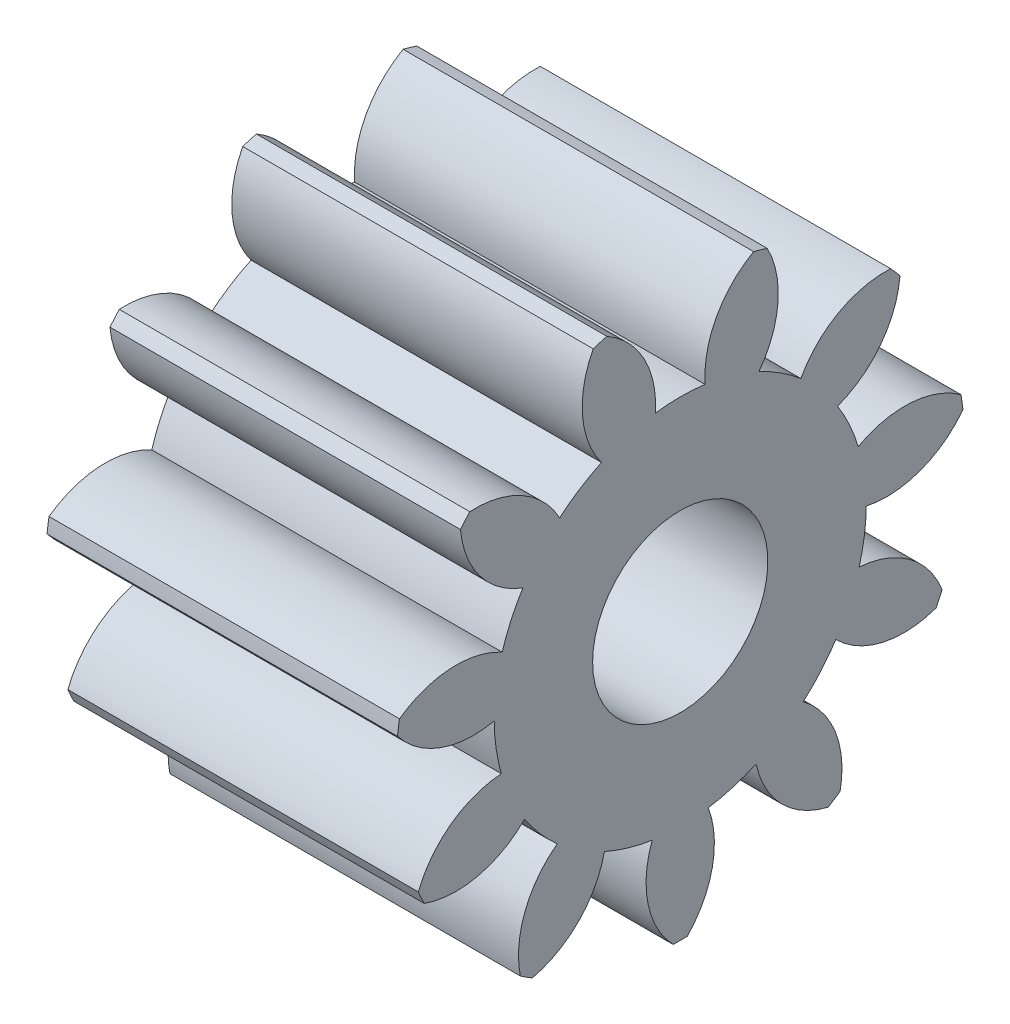
SolidWorks part; units mm, degrees
ref_plane "Plane1" through (0, 0, 0) normal (0, 0, 1) x (1, 0, 0)
ref_plane "Plane2" through (0, 0, 0) normal (0, 1, 0) x (1, 0, 0)
ref_plane "Plane3" through (0, 0, 0) normal (1, 0, 0) x (0, 0, -1)
sketch "HoldingSke" plane through (0, 0, 0) normal (0, 1, 0) x (1, 0, 0)
  line L0 (0, 0) -> (3.9265, -0.7632)
  line L1 (-15, 0) -> (100, 0) construction
  line L2 (0, 0) -> (-2.1039, 2.3779)
  line L3 (0, 0) -> (-11.863, 4.5341)
  line L4 (0, 0) -> (8.4773, 1.6478)
  line L5 (0, 0) -> (-46.8476, -17.4728)
  line L6 (0, 0) -> (-1.6579, -1.1186)
  line L7 (-2.1039, 2.3779) -> (8.6586, 51.2059)
  line L8 (-76.2, 54.61) -> (-76.1, 54.61)
  line L9 (-71.009, 38.7566) -> (-53.1078, 45.2721)
  line L10 (-76.2, 71.12) -> (104.1128, 71.12)
  line L11 (0, 0) -> (-2, 0)
  line L12 (-76.2, 101.6) -> (-76.192, 101.6)
  line L13 (24.9733, 27.94) -> (52.9518, 28.4284)
  line L14 (24.9733, 27.94) -> (24.9743, 27.94)
  line L15 (24.9733, 27.94) -> (100.4006, 29.5858)
  line L16 (-63.627, -0.25) -> (-12.827, -0.25)
  circle A0 centre (0, 0) radius 0.5
  circle A1 centre (0, 0) radius 1.0615
  circle A2 centre (0, 0) radius 37.5
  circle A3 centre (0, 0) radius 0.5
  dimension "MHD" = 2.123
  dimension "Hub_dia" = 75
  dimension "Bore" = 1
  dimension "MBD" = 1
  dimension "Num_teeth" = 11
  dimension "Pitch" = 4
  dimension "Overall_len" = 50
  dimension "Show_teeth" = 11
  dimension "Thickness" = 2
  dimension "OAL" = 50.0001
  dimension "T_dim" = 0.1
  dimension "Ap" = 20
  dimension "H" = 19.05
  dimension "Pitch_radius" = 180.3128
  dimension "Width" = 2
  dimension "Backlash" = 0.008
  dimension "Addendum_fac" = 1
  dimension "Dedendum_fac" = 1.25
  dimension "Clearance_fac" = 0.25
  dimension "Dedendum_add" = 0.001
  dimension "Module" = 0.25
sketch "BasProSke" plane through (0, 0, 0) normal (0, 1, 0) x (1, 0, 0)
  line L0 (-10, 0) -> (60, 0) construction
  line L1 (0, 0) -> (0, 1.625)
  line L2 (0, 0) -> (2, 0)
  line L3 (2, 0) -> (2, 1.625)
  line L4 (2, 1.625) -> (0, 1.625)
  dimension "Thickness" = 2
  dimension "Diameter" = 3.25
revolve "Base-Revolve" add sketch "BasProSke" angle 360 about L0
sketch "TooCutSke" plane through (0, 0, 0) normal (1, 0, 0) x (0, 0, -1)
  line L1 (0, 0) -> (0, 107) construction
  line L2 (0, 0) -> (-0.2097, 1.3589) construction
  line L3 (0, 0) -> (-0.768, 2.6155) construction
  line L4 (-0.2097, 1.3589) -> (-0.384, 1.3077) construction
  arc A0 (0.142, 1.052) -> (-0.142, 1.052) centre (0, 0) ccw
  arc A1 (0.4516, 1.5874) -> (-0.4516, 1.5874) centre (0, 0) ccw
  circle A2 centre (0, 0) radius 1.375 construction
  circle A3 centre (0, 0) radius 1.2921 construction
  arc A4 (-0.142, 1.052) -> (-0.4516, 1.5874) centre (-0.6906, 1.092) ccw
  arc A5 (0.4516, 1.5874) -> (0.142, 1.052) centre (0.6906, 1.092) ccw
  dimension "Root_dia" = 2.123
  dimension "Overcut_dia" = 3.3008
  dimension "Pitch_dia" = 2.75
  dimension "Base_dia" = 2.5842
  dimension "Flank_rad" = 0.55
  dimension "Half_ang" = 16.364
  dimension "Half_CT" = 0.1817
extrude "ToothCut" cut sketch "TooCutSke" along normal through all
fillet "Breaks" [suppressed] radius 0.005
fillet "RootFillets" [suppressed] radius 0.0635
pattern_circular "TeethCuts" count 11 every 32.727 about axis through (-10, 0, 0) along (1, 0, 0) of "ToothCut", "RootFillets", "Breaks"
sketch "HubNeaOneSke" plane through (0, 0, 0) normal (-1, 0, 0) x (0, 0, 1)
  circle A0 centre (0, 0) radius 1.0615
  dimension "Diameter" = 2.123
extrude "HubNearOne" [suppressed] add sketch "HubNeaOneSke" along normal blind 48.0001
sketch "HubNeaBotSke" plane through (0, 0, 0) normal (-1, 0, 0) x (0, 0, 1)
  circle A0 centre (0, 0) radius 1.0615
  dimension "Diameter" = 2.123
extrude "HubNearBoth" [suppressed] add sketch "HubNeaBotSke" along normal blind 24
ref_plane "FarPln" through (2, 0, 0) normal (1, 0, 0) x (0, 0, -1)
sketch "HubFarSke" plane through (2, 0, 0) normal (1, 0, 0) x (0, 0, -1)
  circle A0 centre (0, 0) radius 1.0615
  dimension "Diameter" = 2.123
extrude "HubFar" [suppressed] add sketch "HubFarSke" along normal blind 24
sketch "BorSke" plane through (0, 0, 0) normal (1, 0, 0) x (0, 0, -1)
  circle A0 centre (0, 0) radius 0.5
  dimension "Diameter" = 1
extrude "Bore" cut sketch "BorSke" along normal mid plane 100.0001
sketch "KeySke" plane through (0, 0, 0) normal (1, 0, 0) x (0, 0, -1)
  line L0 (-0.05, 0) -> (-0.05, 0.6)
  line L1 (-0.05, 0.6) -> (0.05, 0.6)
  line L2 (0.05, 0.6) -> (0.05, 0)
  line L3 (0, 0) -> (0, 34) construction
  line L4 (-0.05, 0) -> (0.05, 0)
  dimension "Offset" = 0.6
  dimension "Width" = 0.1
extrude "Keyway" [suppressed] cut sketch "KeySke" along normal mid plane 100.0001
pattern_circular "Keyway2" [suppressed] count 2 every 90 about axis through (-10, 0, 0) along (1, 0, 0)
equation "' \"Module@HoldingSke\" = 6.35"
equation "' \"Num_teeth@HoldingSke\" = 12"
equation "' \"Ap@HoldingSke\" =  20"
equation "' \"Ap@HoldingSke\" = 20"
equation "' \"Width@HoldingSke\" = 0.5 * 25.4"
equation "' \"Hub_dia@HoldingSke\"= 1 * 25.4"
equation "' \"Hub_dia@HoldingSke\" = 1 * 25.4"
equation "' \"Overall_len@HoldingSke\" = 1.0 * 25.4"
equation "' \"Bore@HoldingSke\" = 0.75 * 25.4"
equation "' \"T_dim@HoldingSke\" = 0.1 * 25.4"
equation "' \"Width@KeySke\" = 0.25 * 25.4"
equation "' \"Show_teeth@HoldingSke\" = 13"
equation "' \"Backlash@HoldingSke\" = 0.009 * 25.4"
equation "' \"Addendum_fac@HoldingSke\" = 1.0"
equation "' \"Dedendum_fac@HoldingSke\" = 1.25"
equation "' \"Dedendum_add@HoldingSke\" = 0.00005 * 25.4"
equation "' \"Clearance_fac@HoldingSke\" = 0.25"
equation "\"Pitch@HoldingSke\" = 1 / \"Module@HoldingSke\""
equation "\"Overcut_dia@TooCutSke\" = (\"Num_teeth@HoldingSke\" + 2 * \"Addendum_fac@HoldingSke\") / \"Pitch@HoldingSke\" + 0.002 * 25.4"
equation "\"Pitch_dia@TooCutSke\" = \"Num_teeth@HoldingSke\" / \"Pitch@HoldingSke\""
equation "\"Base_dia@TooCutSke\" = \"Num_teeth@HoldingSke\" / \"Pitch@HoldingSke\" * cos((\"Ap@HoldingSke\"  * 3.14159265 / 180))"
equation "\"Root_dia@TooCutSke\" = (\"Num_teeth@HoldingSke\" + 2) / \"Pitch@HoldingSke\" - 2 * (\"Addendum_fac@HoldingSke\" + \"Dedendum_fac@HoldingSke\") / \"Pitch@HoldingSke\" - \"Dedendum_add@HoldingSke\" * 2"
equation "\"Half_ang@TooCutSke\" = 180 / \"Num_teeth@HoldingSke\""
equation "\"Half_CT@TooCutSke\" = \"Num_teeth@HoldingSke\" / \"Pitch@HoldingSke\" * sin((3.14159265 / 2 / \"Num_teeth@HoldingSke\")) / 2 - 7 * \"Backlash@HoldingSke\" / 4"
equation "\"Flank_rad@TooCutSke\" = \"Num_teeth@HoldingSke\" / \"Pitch@HoldingSke\" / 5"
equation "\"Radius@RootFillets\" = \"Clearance_fac@HoldingSke\" / \"Pitch@HoldingSke\" + \"Dedendum_add@HoldingSke\""
equation "\"Break_rad@Breaks\" = 0.02 / \"Pitch@HoldingSke\""
equation "\"Thickness@HoldingSke\" = \"Width@HoldingSke\""
equation "\"OAL@HoldingSke\" = \"Thickness@HoldingSke\""
equation "\"MHD@HoldingSke\" = (\"Num_teeth@HoldingSke\" + 2) / \"Pitch@HoldingSke\" - 2 * (\"Addendum_fac@HoldingSke\" + \"Dedendum_fac@HoldingSke\")  / \"Pitch@HoldingSke\" - \"Dedendum_add@HoldingSke\" * 2"
equation "\"MBD@HoldingSke\" = (\"Num_teeth@HoldingSke\" + 2) / \"Pitch@HoldingSke\" - 2 * (\"Addendum_fac@HoldingSke\" + \"Dedendum_fac@HoldingSke\")  / \"Pitch@HoldingSke\" - \"Dedendum_add@HoldingSke\" * 2 - 0.002 * 25.4"
equation "\"MHD@HoldingSke\" = ((sgn( \"MHD@HoldingSke\" - \"Hub_dia@HoldingSke\" )-1)*( \"MHD@HoldingSke\" - \"Hub_dia@HoldingSke\" ))/-2+ \"Hub_dia@HoldingSke\""
equation "\"MBD@HoldingSke\" = ((sgn( \"MBD@HoldingSke\" - \"Bore@HoldingSke\" )-1)*( \"MBD@HoldingSke\" - \"Bore@HoldingSke\" ))/-2+ \"Bore@HoldingSke\""
equation "\"OAL@HoldingSke\" = ((sgn( \"OAL@HoldingSke\" - \"Overall_len@HoldingSke\" )+1)*( \"OAL@HoldingSke\" - \"Overall_len@HoldingSke\" ))/2 + \"Overall_len@HoldingSke\" + 0.000002 * 25.4"
equation "\"Num_teeth@TeethCuts\" = int( \"Show_teeth@HoldingSke\" ) + 1"
equation "\"Num_teeth@TeethCuts\" = ((sgn( \"Num_teeth@TeethCuts\" - \"Num_teeth@HoldingSke\" )-1)*( \"Num_teeth@TeethCuts\" - \"Num_teeth@HoldingSke\" ))/-2+ \"Num_teeth@HoldingSke\""
equation "\"Num_teeth@TeethCuts\" = ((sgn( \"Num_teeth@TeethCuts\" - 2.0)+1)*( \"Num_teeth@TeethCuts\" - 2.0))/2 +2.0"
equation "\"Angle@TeethCuts\" = 360.0 / \"Num_teeth@HoldingSke\""
equation "\"Diameter@BasProSke\" = (\"Num_teeth@HoldingSke\" + 2 * \"Addendum_fac@HoldingSke\") / \"Pitch@HoldingSke\""
equation "\"Thickness@BasProSke\"  = \"Thickness@HoldingSke\""
equation "' \"Fillet_rad@BasProSke\" =  \"Thickness@HoldingSke\" * 0.05"
equation "' \"Fillet_rad@BasProSke\" = \"Thickness@HoldingSke\" * 0.05"
equation "\"MHD@HoldingSke\" = ((sgn( \"MHD@HoldingSke\" - \"Root_dia@TooCutSke\" )-1)*( \"MHD@HoldingSke\" - \"Root_dia@TooCutSke\" ))/-2+ \"Root_dia@TooCutSke\""
equation "\"Diameter@HubNeaOneSke\" = \"MHD@HoldingSke\""
equation "\"Length@HubNearOne\" = \"OAL@HoldingSke\" - \"Thickness@BasProSke\""
equation "\"Diameter@HubNeaBotSke\" = \"MHD@HoldingSke\""
equation "\"Length@HubNearBoth\" = ( \"OAL@HoldingSke\" - \"Thickness@BasProSke\" ) / 2.0"
equation "\"Thickness@FarPln\" = \"Thickness@BasProSke\""
equation "\"Diameter@HubFarSke\" = \"MHD@HoldingSke\""
equation "\"Length@HubFar\" = ( \"OAL@HoldingSke\" - \"Thickness@BasProSke\" ) / 2.0"
equation "\"Diameter@BorSke\" = \"MBD@HoldingSke\""
equation "\"D1@Bore\" = \"OAL@HoldingSke\" * 2.0"
equation "\"D1@Keyway\" = \"OAL@HoldingSke\" * 2.0"
equation "\"Offset@KeySke\" = \"T_dim@HoldingSke\" + \"MBD@HoldingSke\" / 2.0"
